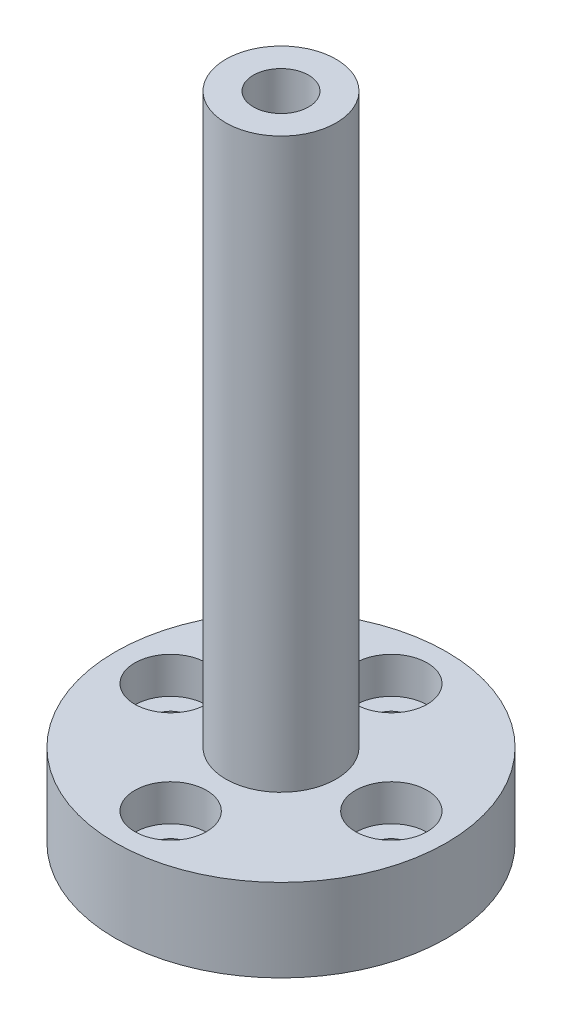
SolidWorks part; units mm, degrees
material "1.0045 (S355JR)"
ref_plane "Front Plane" through (0, 0, 0) normal (0, 0, 1) x (1, 0, 0)
ref_plane "Top Plane" through (0, 0, 0) normal (0, 1, 0) x (1, 0, 0)
ref_plane "Right Plane" through (0, 0, 0) normal (1, 0, 0) x (0, 0, -1)
sketch "Sketch1" plane through (0, 0, 0) normal (0, 1, 0) x (1, 0, 0)
  circle A0 centre (0, 0) radius 30
  dimension "D1" = 60
extrude "Boss-Extrude1" add sketch "Sketch1" along normal blind 15
sketch "Sketch2" plane through (0, 15, 0) normal (0, 1, 0) x (1, 0, 0)
  circle A0 centre (0, 0) radius 10
  dimension "D1" = 20
extrude "Boss-Extrude2" add sketch "Sketch2" along normal blind 103
sketch "Sketch4" plane through (0, 0, 0) normal (0, -1, 0) x (1, 0, 0)
  circle A0 centre (0, 0) radius 7.25
  dimension "D1" = 14.5
extrude "Cut-Extrude1" cut sketch "Sketch4" against normal blind 57
sketch "Sketch5" plane through (0, 57, 0) normal (0, -1, 0) x (1, 0, 0)
  circle A0 centre (0, 0) radius 5
  dimension "D1" = 10
extrude "Cut-Extrude2" cut sketch "Sketch5" against normal through all
sketch "Sketch7" plane through (0, 15, 0) normal (0, 1, 0) x (1, 0, 0)
  circle A0 centre (0, -20) radius 6.5
  point P9 (0, 0)
  point P13 (0, 0)
  dimension "D2" = 13
  dimension "D1" = 20
extrude "Cut-Extrude3" cut sketch "Sketch7" against normal blind 6.6
sketch "Sketch8" plane through (0, 8.4, 0) normal (0, 1, 0) x (1, 0, 0)
  circle A0 centre (0, -20) radius 3.2
  dimension "D1" = 6.4
extrude "Cut-Extrude4" cut sketch "Sketch8" against normal through all
pattern_circular "CirPattern1" count 4 over 360 about axis through (0, 0, 0) along (0, 1, 0) of "Cut-Extrude4", "Cut-Extrude3"
